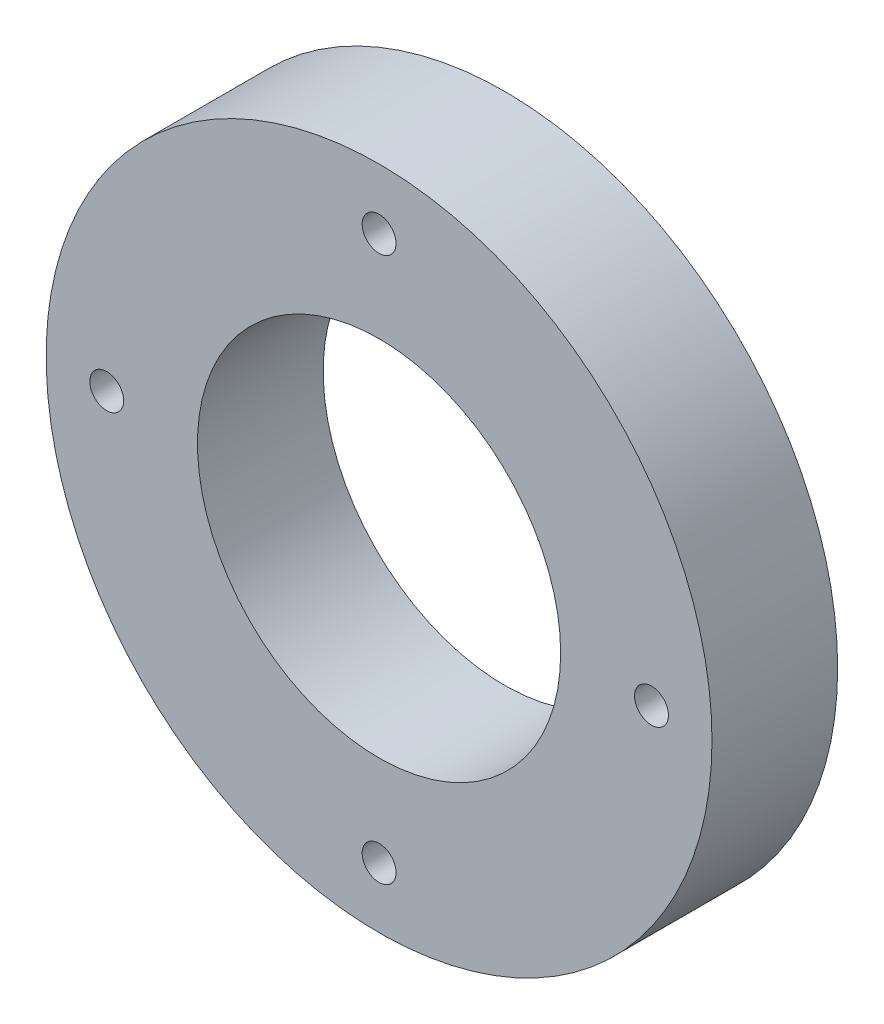
SolidWorks part; units mm, degrees
ref_plane "Front Plane" through (0, 0, 0) normal (0, 0, 1) x (1, 0, 0)
ref_plane "Top Plane" through (0, 0, 0) normal (0, 1, 0) x (1, 0, 0)
ref_plane "Right Plane" through (0, 0, 0) normal (1, 0, 0) x (0, 0, -1)
sketch "Sketch1" plane through (0, 0, 0) normal (0, 0, 1) x (1, 0, 0)
  line L0 (0, 28.575) -> (0, 0) construction
  circle A0 centre (0, 0) radius 34.925
  circle A1 centre (0, 0) radius 19.05
  circle A2 centre (0, 28.575) radius 1.778
  circle A3 centre (28.575, 0) radius 1.778
  circle A4 centre (0, -28.575) radius 1.778
  circle A5 centre (-28.575, 0) radius 1.778
  dimension "D1" = 69.85
  dimension "D2" = 38.1
  dimension "D3" = 3.556
  dimension "D5" = 28.575
  dimension "D4" = 4
extrude "Boss-Extrude1" add sketch "Sketch1" along normal blind 13.1826
